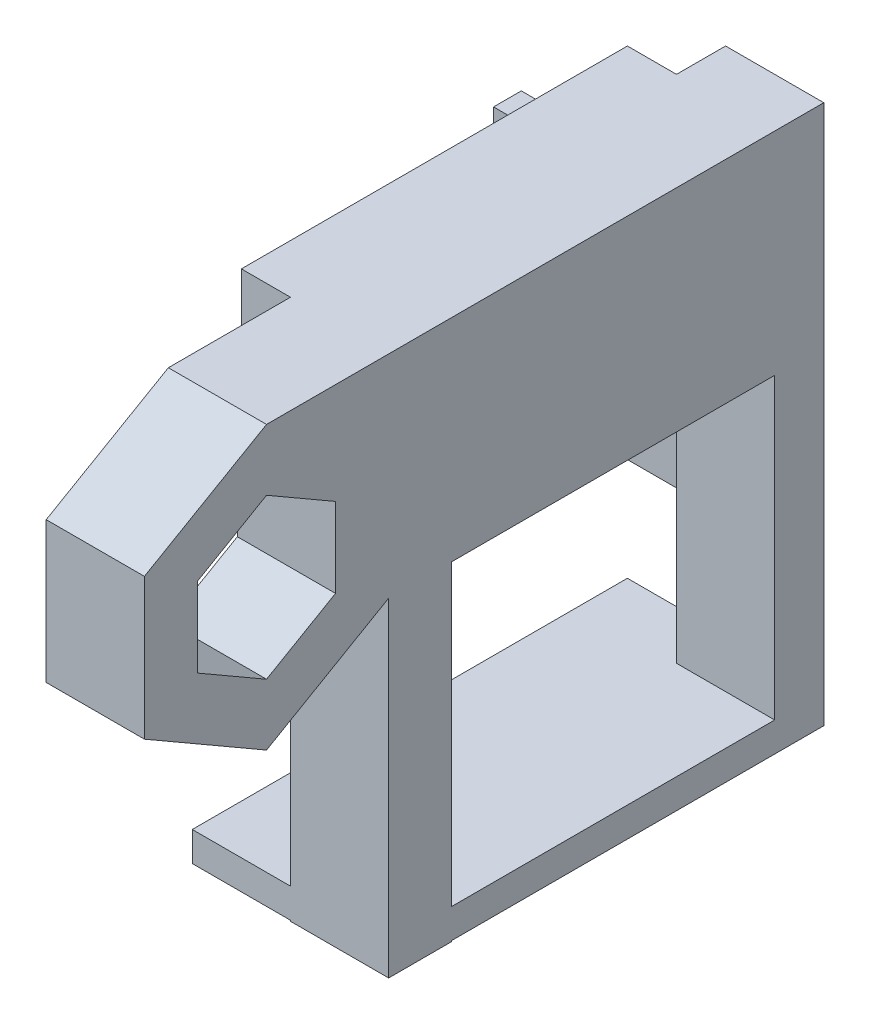
SolidWorks part; units mm, degrees
ref_plane "Front Plane" through (0, 0, 0) normal (0, 0, 1) x (1, 0, 0)
ref_plane "Top Plane" through (0, 0, 0) normal (0, 1, 0) x (1, 0, 0)
ref_plane "Right Plane" through (0, 0, 0) normal (1, 0, 0) x (0, 0, -1)
sketch "Sketch2" plane through (0, 0, 0) normal (1, 0, 0) x (0, 0, -1)
  line L0 (0, 8.2416) -> (0, 14.5916)
  line L1 (0, 8.2416) -> (-7.1374, 4.1208)
  line L2 (-7.1374, 4.1208) -> (-7.1374, -4.1208)
  line L3 (-7.1374, -4.1208) -> (0, -8.2416)
  line L4 (0, -8.2416) -> (7.1374, -4.1208)
  line L5 (7.1374, -4.1208) -> (7.1374, 4.1208)
  line L6 (7.1374, 4.1208) -> (0, 8.2416)
  line L8 (0, 14.5916) -> (-12.6367, 7.2958)
  line L9 (-12.6367, 7.2958) -> (-12.6367, -7.2958)
  line L10 (-12.6367, -7.2958) -> (0, -14.5916)
  line L11 (0, -14.5916) -> (12.6367, -7.2958)
  line L12 (12.6367, -7.2958) -> (12.6367, 7.2958)
  line L13 (12.6367, 7.2958) -> (0, 14.5916)
  circle A0 centre (0, 0) radius 7.1374 construction
  circle A1 centre (0, 0) radius 12.6367 construction
extrude "Boss-Extrude1" add sketch "Sketch2" along normal blind 10.16
sketch "Sketch3" plane through (0, 0, 0) normal (1, 0, 0) x (0, 0, -1)
  line L0 (12.6367, -7.2958) -> (52.578, -7.2958)
  line L1 (0, 14.5916) -> (52.578, 14.5916)
  line L2 (52.578, -7.2958) -> (52.578, 14.5916)
  line L9 (12.6367, 7.2958) -> (0, 14.5916)
  line L10 (0, 14.5916) -> (-12.6367, 7.2958)
  line L11 (-12.6367, 7.2958) -> (-12.6367, -7.2958)
  line L12 (-12.6367, -7.2958) -> (0, -14.5916)
  line L13 (0, -14.5916) -> (12.6367, -7.2958)
  line L14 (12.6367, -7.2958) -> (12.6367, 7.2958)
  line L15 (12.6367, 7.2958) -> (0, 14.5916)
  line L20 (12.6367, -7.2958) -> (12.6367, 7.2958)
  dimension "D1" = 0
extrude "Boss-Extrude2" add sketch "Sketch3" along normal blind 10.16
sketch "Sketch4" plane through (0, 0, 0) normal (-1, 0, 0) x (0, 0, 1)
  line L1 (-52.578, 14.5916) -> (-12.6367, 14.5916)
  line L2 (-52.578, 14.5916) -> (-52.578, 4.1208)
  line L3 (-52.578, 4.1208) -> (-12.6367, 4.1208)
  line L4 (-12.6367, 14.5916) -> (-12.6367, 4.1208)
extrude "Boss-Extrude3" add sketch "Sketch4" along normal blind 5.08
sketch "Sketch6" plane through (0, 0, -52.578) normal (0, 0, -1) x (-1, 0, 0)
  line L1 (-10.16, 14.5916) -> (0, 14.5916)
  line L2 (-10.16, 14.5916) -> (-10.16, -41.2382)
  line L3 (-10.16, -41.2382) -> (0, -41.2382)
  line L4 (0, 14.5916) -> (0, -41.2382)
extrude "Boss-Extrude5" add sketch "Sketch6" along normal blind 5.08
sketch "Sketch9" plane through (0, -7.2958, 0) normal (0, -1, 0) x (-1, 0, 0)
  line L0 (-10.16, 12.6367) -> (-10.16, 52.578) construction
  line L1 (0, 12.6367) -> (-10.16, 12.6367)
  line L2 (0, 12.6367) -> (0, 19.1149)
  line L3 (0, 19.1149) -> (-10.16, 19.1149)
  line L4 (-10.16, 12.6367) -> (-10.16, 19.1149)
extrude "Boss-Extrude6" add sketch "Sketch9" along normal blind 34.036
sketch "Sketch12" plane through (0, 0, 0) normal (-1, 0, 0) x (0, 0, 1)
  line L0 (-12.6367, -41.3318) -> (-12.6367, -7.2958) construction
  line L1 (-57.658, -41.2382) -> (-12.6367, -41.2382)
  line L2 (-57.658, -41.2382) -> (-57.658, -38.1823)
  line L3 (-57.658, -38.1823) -> (-12.6367, -38.1823)
  line L4 (-12.6367, -41.2382) -> (-12.6367, -38.1823)
extrude "Boss-Extrude7" add sketch "Sketch12" along normal blind 10.16
sketch "Sketch13" plane through (0, 0, -52.578) normal (0, 0, 1) x (1, 0, 0)
  line L1 (10.16, -41.2382) -> (0, -41.2382)
  line L2 (10.16, -41.2382) -> (10.16, -38.1823)
  line L3 (10.16, -38.1823) -> (0, -38.1823)
  line L4 (0, -41.2382) -> (0, -38.1823)
extrude "Boss-Extrude8" add sketch "Sketch13" along normal blind 33.528
sketch "Sketch16" plane through (0, 0, 0) normal (-1, 0, 0) x (0, 0, 1)
  line L0 (-57.658, -38.1823) -> (-57.658, 14.5916) construction
  line L1 (-57.658, -24.6806) -> (-54.788, -24.6806)
  line L2 (-57.658, -24.6806) -> (-57.658, 0)
  line L3 (-57.658, 0) -> (-54.788, 0)
  line L4 (-54.788, -24.6806) -> (-54.788, 0)
extrude "Boss-Extrude9" add sketch "Sketch16" along normal blind 21.1391
